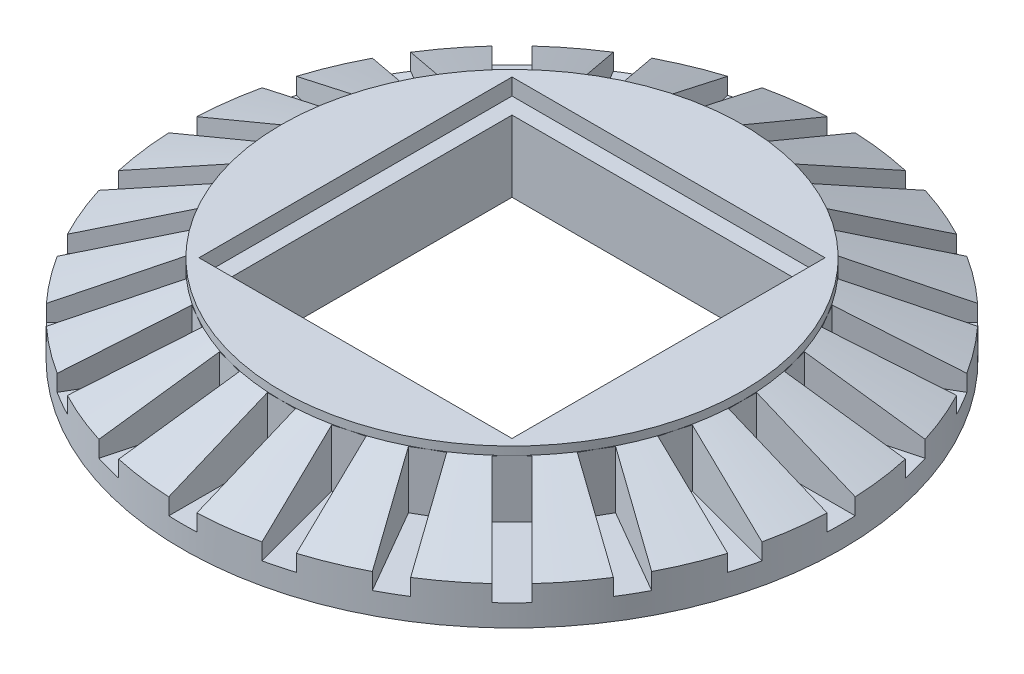
SolidWorks part; units mm, degrees
ref_plane "Front" through (0, 0, 0) normal (0, 0, 1) x (1, 0, 0)
ref_plane "Top" through (0, 0, 0) normal (0, 1, 0) x (1, 0, 0)
ref_plane "Right" through (0, 0, 0) normal (1, 0, 0) x (0, 0, -1)
sketch "Sketch2" plane through (0, 0, 0) normal (0, 0, 1) x (1, 0, 0)
  line L0 (0, 0) -> (31.75, 0)
  line L1 (31.75, 0) -> (31.75, 1.5875)
  line L2 (31.75, 1.5875) -> (22.225, 5.5563)
  line L3 (22.225, 5.5563) -> (22.225, 6.35)
  line L4 (22.225, 6.35) -> (0, 6.35)
  line L5 (0, 6.35) -> (0, 0)
  circle A0 centre (23.4156, 6.35) radius 1.1906 construction
  circle A1 centre (26.5112, 6.35) radius 2.3812 construction
  dimension "D1" = 2.3813
  dimension "D6" = 4.7625
  dimension "D2" = 22.225
  dimension "D3" = 6.35
  dimension "D4" = 4.7625
  dimension "D5" = 9.525
revolve "Revolve1" add sketch "Sketch2" angle 360 about L5
sketch "Sketch3" plane through (0, 0, 0) normal (0, 0, 1) x (1, 0, 0)
  line L0 (22.225, 6.35) -> (31.75, 2.3813)
  line L1 (0, 0) -> (0, 9.5419)
  line L3 (31.75, 1.5875) -> (22.225, 5.5563) construction
  line L6 (31.75, 2.3813) -> (31.75, 0)
  line L7 (31.75, 0) -> (22.225, 0)
  line L8 (-31.75, 0) -> (31.75, 0) construction
  line L9 (22.225, 0) -> (22.225, 6.35)
sketch "Sketch15" plane through (0, 6.35, 0) normal (0, 1, 0) x (1, 0, 0)
  line L1 (13.4937, -13.4937) -> (-13.4937, -13.4938)
  line L2 (13.4937, -13.4937) -> (13.4937, 13.4937)
  line L3 (13.4937, 13.4937) -> (-13.4937, 13.4937)
  line L4 (-13.4937, -13.4938) -> (-13.4937, 13.4937)
  line L5 (13.4937, -13.4937) -> (-13.4937, 13.4937) construction
  line L6 (13.4937, 13.4937) -> (-13.4937, -13.4938) construction
  point P0 (0, 0)
  dimension "D1" = 26.9875
sketch "Sketch16" plane through (0, 6.35, 0) normal (0, 1, 0) x (1, 0, 0)
  line L1 (15.0812, -15.0812) -> (-15.0812, -15.0813)
  line L2 (15.0812, -15.0812) -> (15.0812, 15.0813)
  line L3 (15.0812, 15.0813) -> (-15.0812, 15.0812)
  line L4 (-15.0812, -15.0813) -> (-15.0812, 15.0812)
  line L5 (15.0812, -15.0812) -> (-15.0812, 15.0812) construction
  line L6 (15.0812, 15.0813) -> (-15.0812, -15.0813) construction
  point P0 (0, 0)
  point P6 (-15.0812, 14.0709)
  dimension "D1" = 30.1625
extrude "Cut-Extrude1" cut sketch "Sketch3" against normal mid plane 2.7 contours L0 L6 L7 L9
pattern_circular "CirPattern1" count 24 over 360 about axis through (0, 0, 0) along (0, 1, 0) of "Cut-Extrude1"
sketch "Sketch17" plane through (0, 0, 0) normal (0, -1, 0) x (1, 0, 0)
  circle A0 centre (0, 0) radius 31.75
extrude "Boss-Extrude1" add sketch "Sketch17" along normal blind 2.1
extrude "Cut-Extrude2" cut sketch "Sketch15" against normal through all contours L4 L3 L2 L1
extrude "Cut-Extrude3" cut sketch "Sketch16" against normal blind 1.5875 contours L4 L3 L2 L1
equation "\"D1@Cut-Extrude1\"=.9mm+1.5*1.2mm"
